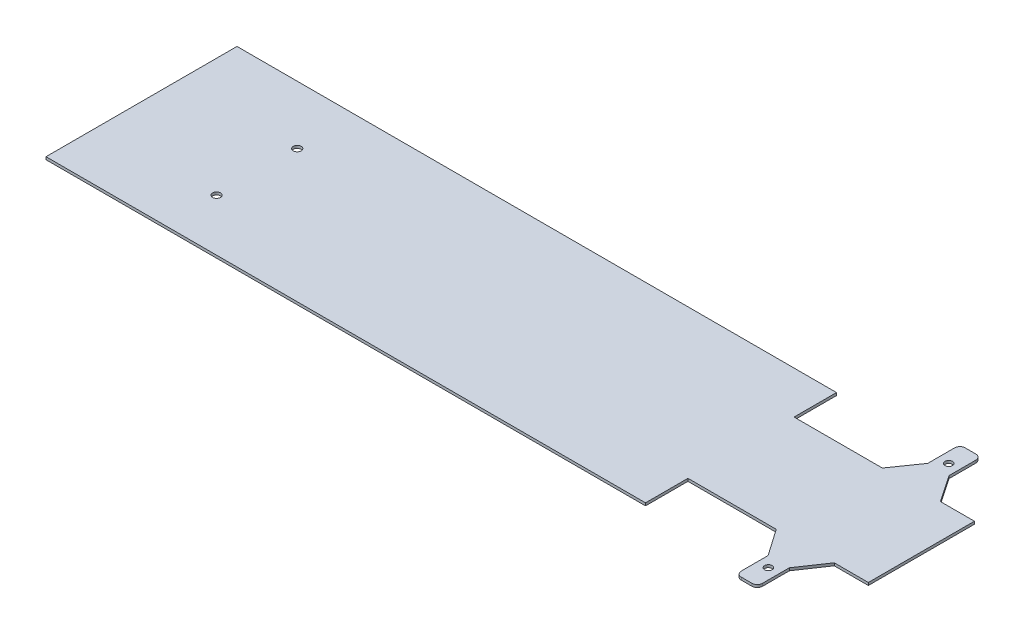
SolidWorks part; units mm, degrees
ref_plane "Front" through (0, 0, 0) normal (0, 0, 1) x (1, 0, 0)
ref_plane "Top" through (0, 0, 0) normal (0, 1, 0) x (1, 0, 0)
ref_plane "Right" through (0, 0, 0) normal (1, 0, 0) x (0, 0, -1)
sketch "Sketch1" plane through (0, 0, 0) normal (0, 1, 0) x (1, 0, 0)
  line L0 (-415.5424, 422.6316) -> (-351.2965, 422.6316)
  line L1 (-691.2965, 422.6316) -> (-524.869, 422.6316)
  line L3 (-691.2965, 222.6316) -> (-524.869, 222.6316)
  line L4 (-351.2965, 422.6316) -> (-351.2965, 222.6316)
  line L6 (-489.7086, 473.1316) -> (-489.7086, 523.6316)
  line L7 (-479.7086, 533.6316) -> (-459.7086, 533.6316)
  line L8 (-449.7086, 473.1316) -> (-449.7086, 523.6316)
  line L9 (-449.7086, 172.1316) -> (-415.5424, 222.6316)
  line L10 (-449.7086, 172.1316) -> (-449.7086, 121.6316)
  line L11 (-479.7086, 111.6316) -> (-459.7086, 111.6316)
  line L12 (-489.7086, 172.1316) -> (-489.7086, 121.6316)
  line L13 (-415.5424, 222.6316) -> (-351.2965, 222.6316)
  line L14 (-691.2965, 222.6316) -> (-691.2965, 142.6316)
  line L15 (-691.2965, 502.6316) -> (-1821.2965, 502.6316)
  line L16 (-691.2965, 502.6316) -> (-691.2965, 422.6316)
  line L17 (-691.2965, 142.6316) -> (-1821.2965, 142.6316)
  line L18 (-1821.2965, 502.6316) -> (-1821.2965, 142.6316)
  line L19 (-489.7086, 172.1316) -> (-524.869, 222.6316)
  line L20 (-351.2965, 322.6316) -> (-691.2965, 322.6316) construction
  line L21 (-489.7086, 473.1316) -> (-524.869, 422.6316)
  line L22 (-449.7086, 473.1316) -> (-415.5424, 422.6316)
  arc A0 (-459.7086, 533.6316) -> (-449.7086, 523.6316) centre (-459.7086, 523.6316) cw
  arc A1 (-489.7086, 523.6316) -> (-479.7086, 533.6316) centre (-479.7086, 523.6316) cw
  arc A2 (-489.7086, 121.6316) -> (-479.7086, 111.6316) centre (-479.7086, 121.6316) ccw
  arc A3 (-459.7086, 111.6316) -> (-449.7086, 121.6316) centre (-459.7086, 121.6316) ccw
  circle A4 centre (-469.7086, 492.6316) radius 7
  circle A5 centre (-469.7086, 152.6316) radius 7
  point P4 (-469.7086, 485.6316)
  point P7 (-469.7086, 159.6316)
  point P10 (-449.7086, 533.6316)
  point P13 (-489.7086, 533.6316)
  point P24 (-489.7086, 111.6316)
  point P25 (-449.7086, 111.6316)
  dimension "D5" = 10
  dimension "D6" = 340
  dimension "D8" = 118.4122
  dimension "D1" = 340
  dimension "D2" = 200
  dimension "D3" = 40
  dimension "D9" = 20
  dimension "D10" = 1130
  dimension "D11" = 360
  dimension "D12" = 80
extrude "Boss-Extrude1" add sketch "Sketch1" along normal blind 5
sketch "Sketch2" plane through (0, 5, 0) normal (0, 1, 0) x (1, 0, 0)
  circle A0 centre (-1597.7702, 392.5496) radius 7.5
  circle A1 centre (-1597.7702, 240.6077) radius 7.5
  point P4 (-1597.7702, 392.5496)
  point P5 (-1597.7702, 240.6077)
extrude "Cut-Extrude1" cut sketch "Sketch2" against normal blind 10
